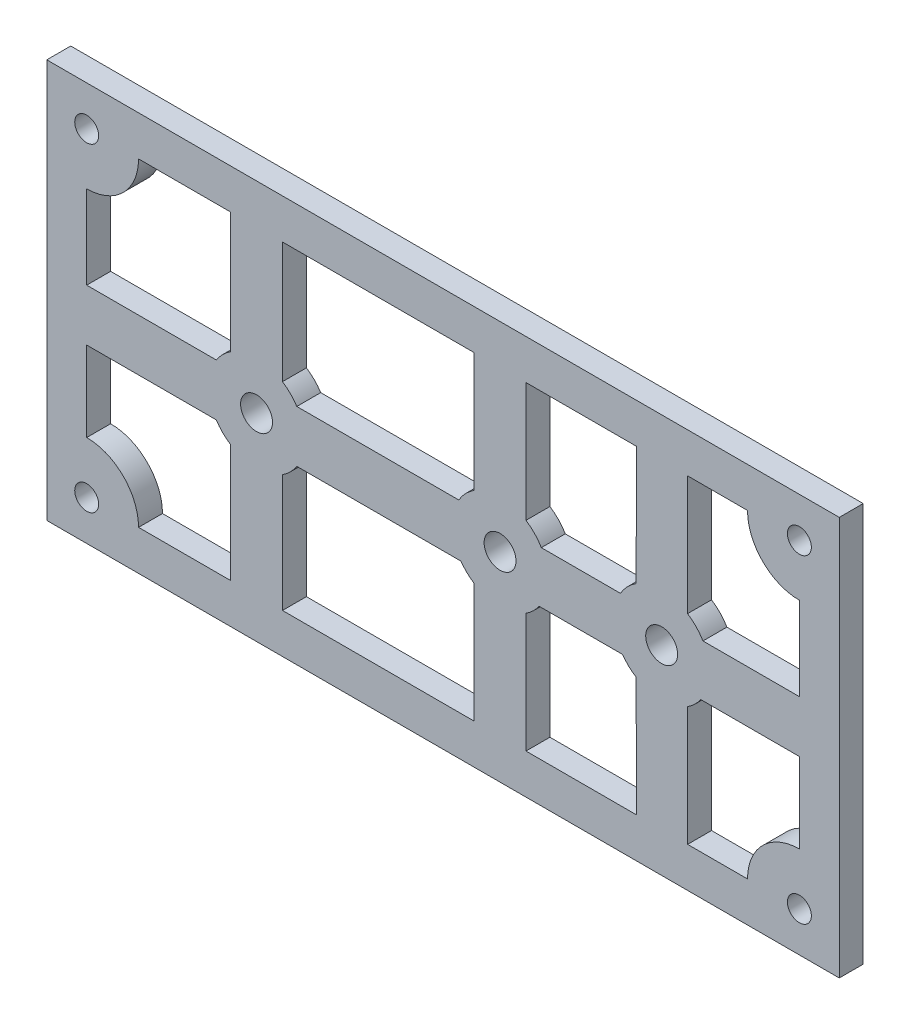
SolidWorks part; units mm, degrees
ref_plane "Front Plane" through (0, 0, 0) normal (0, 0, 1) x (1, 0, 0)
ref_plane "Top Plane" through (0, 0, 0) normal (0, 1, 0) x (1, 0, 0)
ref_plane "Right Plane" through (0, 0, 0) normal (1, 0, 0) x (0, 0, -1)
sketch "Sketch1" plane through (0, 0, 0) normal (0, 0, 1) x (1, 0, 0)
  line L1 (-57.5, -25) -> (57.5, -25)
  line L2 (-57.5, -25) -> (-57.5, 25)
  line L3 (-57.5, 25) -> (57.5, 25)
  line L4 (57.5, -25) -> (57.5, 25)
  line L5 (-57.5, -25) -> (57.5, 25) construction
  line L6 (-57.5, 25) -> (57.5, -25) construction
  point P0 (0, 0)
  dimension "D1" = 115
  dimension "D2" = 50
extrude "Boss-Extrude1" add sketch "Sketch1" along normal blind 3
sketch "Sketch2" plane through (0, 0, 3) normal (0, 0, 1) x (1, 0, 0)
  line L0 (57.5, 25) -> (-57.5, 25) construction
  line L1 (-57.5, 25) -> (-57.5, -25) construction
  circle A0 centre (-52.5, 20) radius 1.5
  dimension "D1" = 3
  dimension "D2" = 5
  dimension "D3" = 5
extrude "Cut-Extrude1" cut sketch "Sketch2" against normal through all and the other way through all
sketch "Sketch3" plane through (0, 0, 3) normal (0, 0, 1) x (1, 0, 0)
  line L0 (57.5, 0) -> (-57.5, 0) construction
  line L1 (57.5, -25) -> (57.5, 25) construction
  line L2 (-57.5, 25) -> (-57.5, -25) construction
sketch "Sketch4" plane through (0, 0, 3) normal (0, 0, 1) x (1, 0, 0)
  circle A0 centre (-31.2105, -0.2094) radius 2
extrude "Cut-Extrude2" cut sketch "Sketch4" against normal through all
sketch "Sketch5" plane through (0, 0, 3) normal (0, 0, 1) x (1, 0, 0)
  circle A0 centre (-0.692, 0) radius 2
extrude "Cut-Extrude3" cut sketch "Sketch5" against normal blind 10
sketch "Sketch6" plane through (0, 0, 3) normal (0, 0, 1) x (1, 0, 0)
  line L0 (57.5, 0) -> (-57.5, 0) construction
  circle A0 centre (19.5658, 0) radius 2
extrude "Cut-Extrude4" cut sketch "Sketch6" against normal blind 10
sketch "Sketch7" plane through (0, 0, 3) normal (0, 0, 1) x (1, 0, 0)
  line L0 (-57.5, -25) -> (57.5, -25) construction
  line L1 (57.5, 25) -> (41.8258, 25)
  line L2 (57.5, 25) -> (57.5, -25)
  line L3 (57.5, -25) -> (41.8258, -25)
  line L4 (41.8258, 25) -> (41.8258, -25)
  circle A0 centre (19.5658, 0) radius 2 construction
  dimension "D1" = 22.26
extrude "Cut-Extrude5" cut sketch "Sketch7" against normal blind 10
ref_plane "Plane1" through (-7.8371, 0, 0) normal (-1, 0, 0) x (0, 0, 1)
ref_plane "Plane2" through (0, 0, 0) normal (0, 1, 0) x (1, 0, 0)
mirror "Mirror1" about plane through (-7.8371, 0, 0) normal (-1, 0, 0) of "Cut-Extrude1"
mirror "Mirror2" about plane through (0, 0, 0) normal (0, 1, 0) of "Mirror1", "Cut-Extrude1"
sketch "Sketch8" plane through (0, 0, 3) normal (0, 0, 1) x (1, 0, 0)
  line L0 (-52.5, -3.4594) -> (-52.5, -13.5)
  line L2 (-52.5, 13.5) -> (-52.5, 3.0406)
  line L3 (-46, -20) -> (-34.4605, -20)
  line L4 (36.8258, 13.5) -> (36.8258, -13.5)
  line L8 (36.8258, 3.0406) -> (36.8258, -3.4594)
  line L9 (-52.5, 3.0406) -> (-36.254, 3.0406)
  line L10 (-52.5, -3.4594) -> (-36.254, -3.4594)
  line L11 (-52.5, 3.0406) -> (-52.5, -3.4594)
  line L12 (-46, 20) -> (-34.4605, 20)
  line L13 (-26.1669, 3.0406) -> (-5.8645, 3.0406)
  line L14 (-26.1669, -3.4594) -> (-5.5942, -3.4594)
  line L15 (-34.4605, -5.253) -> (-34.4605, -20)
  line L16 (-34.4605, 4.8341) -> (-34.4605, 20)
  line L17 (-27.9605, 4.8341) -> (-27.9605, 20)
  line L18 (-27.9605, -5.253) -> (-27.9605, -20)
  line L19 (16.3478, 5.064) -> (16.4419, 20)
  line L20 (-3.942, 5.0436) -> (-3.942, 20)
  line L22 (2.558, 5.0436) -> (2.558, 20)
  line L24 (-3.942, -5.0436) -> (-3.942, -20)
  line L28 (4.2103, -3.4594) -> (14.6636, -3.4594)
  line L29 (2.558, -5.0436) -> (2.558, -20)
  line L30 (4.4806, 3.0406) -> (14.3933, 3.0406)
  line L31 (-27.9605, 20) -> (-3.942, 20)
  line L32 (-27.9605, -20) -> (-3.942, -20)
  line L33 (2.558, -20) -> (16.4419, -20)
  line L34 (2.558, 20) -> (16.4419, 20)
  line L36 (22.8158, 5.0436) -> (22.8158, 20)
  line L37 (16.3478, -5.064) -> (16.4419, -20)
  line L38 (22.8158, -5.0436) -> (22.8158, -20)
  line L39 (24.4681, -3.4594) -> (36.8258, -3.4594)
  line L40 (24.7384, 3.0406) -> (36.8258, 3.0406)
  line L41 (22.8158, -20) -> (30.3258, -20)
  line L42 (22.8158, 20) -> (30.3258, 20)
  arc A3 (-34.4605, 4.8341) -> (-36.254, 3.0406) centre (-31.2105, -0.2094) ccw
  arc A4 (-5.5942, -3.4594) -> (-3.942, -5.0436) centre (-0.692, 0) ccw
  arc A5 (36.8258, -13.5) -> (30.3258, -20) centre (36.8258, -20) ccw
  arc A6 (-46, -20) -> (-52.5, -13.5) centre (-52.5, -20) ccw
  arc A7 (-52.5, 13.5) -> (-46, 20) centre (-52.5, 20) ccw
  arc A8 (30.3258, 20) -> (36.8258, 13.5) centre (36.8258, 20) ccw
  arc A9 (16.3478, 5.064) -> (14.3933, 3.0406) centre (19.5658, 0) ccw
  arc A10 (-36.254, -3.4594) -> (-34.4605, -5.253) centre (-31.2105, -0.2094) ccw
  arc A11 (-27.9605, -5.253) -> (-26.1669, -3.4594) centre (-31.2105, -0.2094) ccw
  arc A12 (-26.1669, 3.0406) -> (-27.9605, 4.8341) centre (-31.2105, -0.2094) ccw
  arc A13 (-3.942, 5.0436) -> (-5.8645, 3.0406) centre (-0.692, 0) ccw
  arc A14 (4.4806, 3.0406) -> (2.558, 5.0436) centre (-0.692, 0) ccw
  arc A15 (2.558, -5.0436) -> (4.2103, -3.4594) centre (-0.692, 0) ccw
  arc A16 (24.7384, 3.0406) -> (22.8158, 5.0436) centre (19.5658, 0) ccw
  arc A17 (22.8158, -5.0436) -> (24.4681, -3.4594) centre (19.5658, 0) ccw
  arc A18 (14.6636, -3.4594) -> (16.3478, -5.064) centre (19.5658, 0) ccw
  point P25 (-31.2105, -0.2094)
  point P39 (-0.692, 0)
  point P56 (19.5658, 0)
  dimension "D1" = 12
  dimension "D2" = 12
  dimension "D3" = 12
  dimension "D6" = 13
  dimension "D7" = 13
  dimension "D8" = 13
  dimension "D9" = 13
  dimension "D4" = 6.5
extrude "Cut-Extrude6" cut sketch "Sketch8" against normal blind 10 contours A7 L2 L9 A3 L16 L12 | A13 L20 L31 L17 A12 L13 | A14 L30 A9 L19 L34 L22 | A16 L40 L4 A8 L42 L36 | A17 L38 L41 A5 L4 L39 | A18 L28 A15 L29 L33 L37 | A11 L18 L32 L24 A4 L14 | A10 L10 L0 A6 L3 L15
